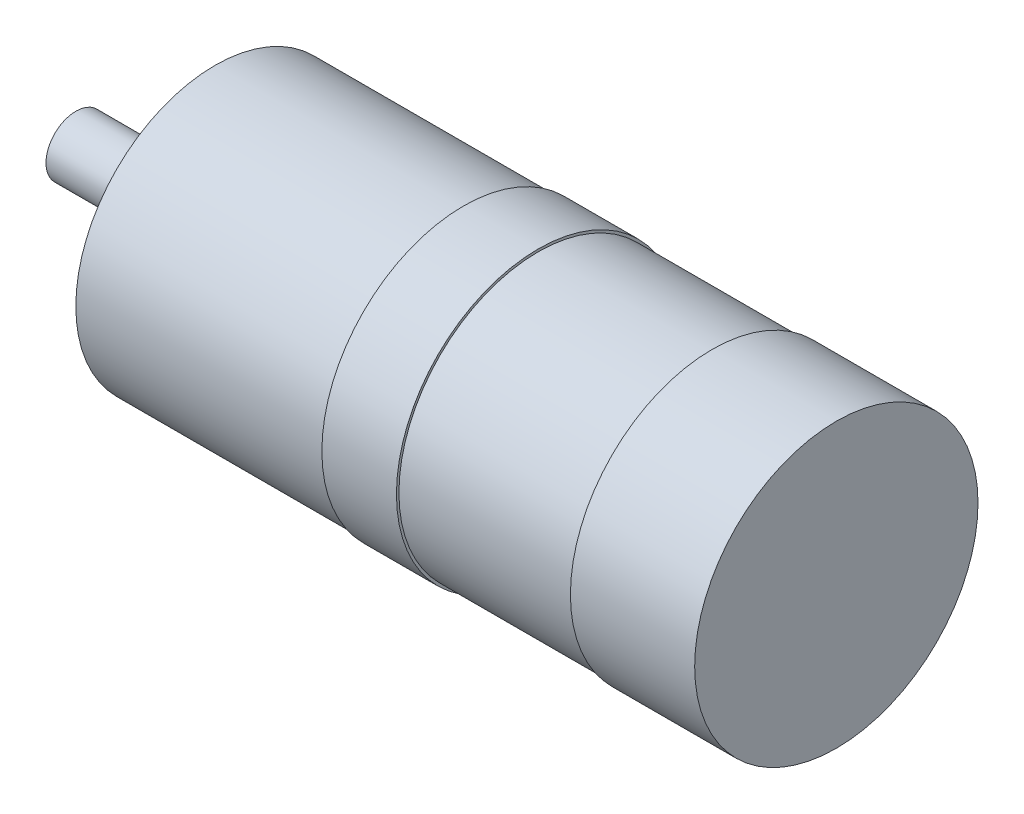
SolidWorks part; units mm, degrees
material "Plain Carbon Steel"
ref_plane "Front Plane" through (0, 0, 0) normal (0, 0, 1) x (1, 0, 0)
ref_plane "Top Plane" through (0, 0, 0) normal (0, 1, 0) x (1, 0, 0)
ref_plane "Right Plane" through (0, 0, 0) normal (1, 0, 0) x (0, 0, -1)
sketch "Sketch1" plane through (0, 0, 0) normal (0, 0, 1) x (1, 0, 0)
  line L0 (0, 0) -> (153, 0)
  line L1 (-903.2374, 0) -> (44258.6317, 0) construction
  line L2 (0, 0) -> (0, 6)
  line L3 (0, 6) -> (26, 6)
  line L4 (26, 6) -> (26, 16)
  line L5 (26, 16) -> (28, 16)
  line L6 (28, 16) -> (28, 28)
  line L7 (28, 28) -> (78, 28)
  line L8 (78, 28) -> (78, 28.5)
  line L9 (78, 28.5) -> (93, 28.5)
  line L10 (93, 28.5) -> (93, 28)
  line L11 (93, 28) -> (128, 28)
  line L12 (128, 28) -> (128, 28.5)
  line L13 (128, 28.5) -> (153, 28.5)
  line L14 (153, 28.5) -> (153, 0)
  point P1 (28, 22)
  dimension "D2" = 28
  dimension "D3" = 2
  dimension "D4" = 32
  dimension "D5" = 56
  dimension "D6" = 57
  dimension "D7" = 125
  dimension "D8" = 75
  dimension "D9" = 15
  dimension "D10" = 25
  dimension "D11" = 12
revolve "Revolve1" add sketch "Sketch1" angle 360 about L1
sketch "Sketch2" plane through (28, 0, 0) normal (-1, 0, 0) x (0, 0, 1)
  circle A0 centre (0, 0) radius 22.5 construction
  circle A1 centre (-15.9099, 15.9099) radius 2.1
  circle A2 centre (15.9099, 15.9099) radius 2.1
  circle A3 centre (15.9099, -15.9099) radius 2.1
  circle A4 centre (-15.9099, -15.9099) radius 2.1
  point P14 (0, 0)
  dimension "D1" = 45
  dimension "D3" = 4.2
  dimension "D2" = 4
extrude "Cut-Extrude1" cut sketch "Sketch2" against normal blind 6.5
sketch "Sketch3" plane through (0, 0, 0) normal (0, 0, 1) x (1, 0, 0)
  line L0 (16, 6) -> (16, -6)
  line L1 (26, 6) -> (0, 6) construction
  line L2 (0, -6) -> (26, -6) construction
  line L3 (26, 6) -> (26, -6) construction
  dimension "D1" = 10
split line "Split Line1"
